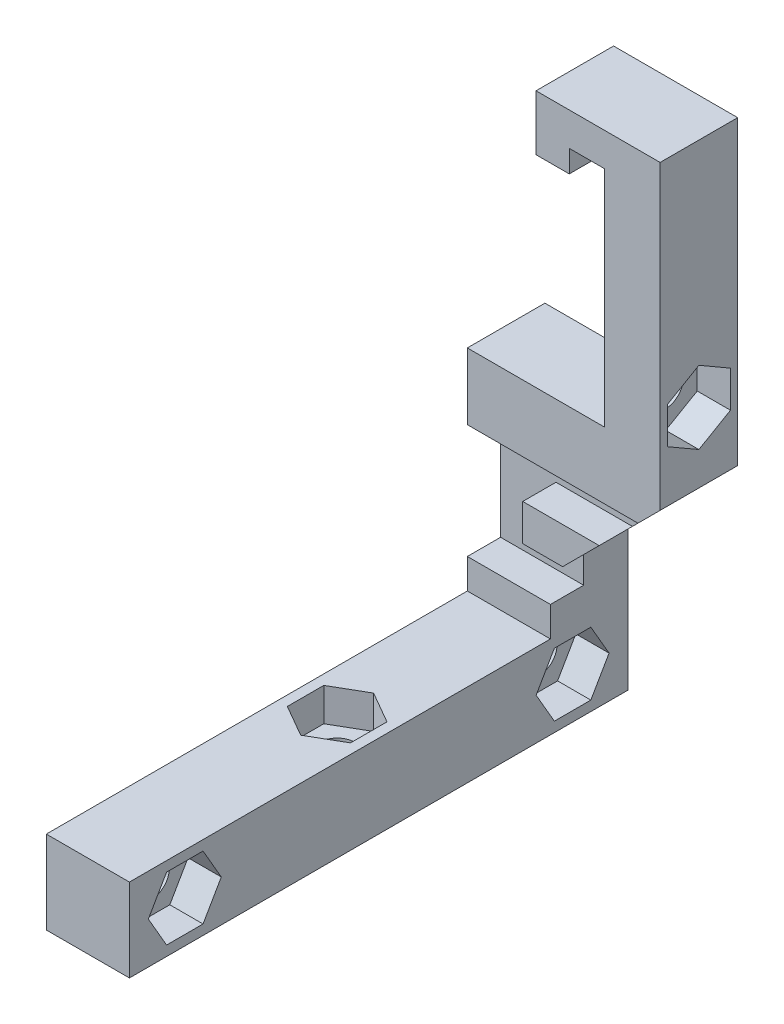
SolidWorks part; units mm, degrees
ref_plane "Alzado" through (0, 0, 0) normal (0, 0, 1) x (1, 0, 0)
ref_plane "Planta" through (0, 0, 0) normal (0, 1, 0) x (1, 0, 0)
ref_plane "Vista lateral" through (0, 0, 0) normal (1, 0, 0) x (0, 0, -1)
sketch "Croquis1" plane through (0, 0, 0) normal (0, 0, 1) x (1, 0, 0)
  line L0 (0, 26.5) -> (0, 0)
  line L1 (0, 0) -> (7.5, 0)
  line L2 (7.5, 0) -> (7.5, 12.6)
  line L3 (0, 26.5) -> (12.4, 26.5)
  line L4 (12.4, 26.5) -> (12.4, 46.7)
  line L5 (12.4, 46.7) -> (9.2, 46.7)
  line L6 (9.2, 46.7) -> (9.2, 44.7)
  line L7 (9.2, 44.7) -> (6.2, 44.7)
  line L8 (6.2, 44.7) -> (6.2, 49.7)
  line L9 (6.2, 49.7) -> (17.4, 49.7)
  line L10 (17.4, 49.7) -> (17.4, 22.5)
  line L11 (17.4, 22.5) -> (7.5, 12.6)
  dimension "D1" = 7.5
  dimension "D2" = 26.5
  dimension "D3" = 12.4
  dimension "D4" = 20.2
  dimension "D5" = 3.2
  dimension "D6" = 2
  dimension "D7" = 3
  dimension "D8" = 3
  dimension "D9" = 5
  dimension "D10" = 135
  dimension "D11" = 4
extrude "Saliente-Extruir1" add sketch "Croquis1" along normal blind 4
sketch "Croquis2" plane through (0, 0, 4) normal (0, 0, 1) x (1, 0, 0)
  line L0 (0, 0) -> (0, 10.2)
  line L1 (0, 10.2) -> (5, 10.2)
  line L2 (5, 10.2) -> (5, 20.5)
  line L3 (5, 20.5) -> (0, 20.5)
  line L4 (0, 20.5) -> (0, 26.5)
  line L12 (12.4, 26.5) -> (0, 26.5)
  line L13 (0, 26.5) -> (0, 0)
  line L14 (0, 0) -> (7.5, 0)
  line L15 (7.5, 0) -> (7.5, 12.6)
  line L16 (7.5, 12.6) -> (17.4, 22.5)
  line L17 (17.4, 22.5) -> (17.4, 49.7)
  line L18 (17.4, 49.7) -> (6.2, 49.7)
  line L19 (6.2, 49.7) -> (6.2, 44.7)
  line L20 (6.2, 44.7) -> (9.2, 44.7)
  line L21 (9.2, 44.7) -> (9.2, 46.7)
  line L22 (9.2, 46.7) -> (12.4, 46.7)
  line L23 (12.4, 46.7) -> (12.4, 26.5)
  line L24 (12.4, 26.5) -> (0, 26.5)
  line L25 (0, 26.5) -> (0, 0) construction
  line L26 (0, 0) -> (7.5, 0)
  line L27 (7.5, 0) -> (7.5, 12.6)
  line L28 (7.5, 12.6) -> (17.4, 22.5)
  line L29 (17.4, 22.5) -> (17.4, 49.7)
  line L30 (17.4, 49.7) -> (6.2, 49.7)
  line L31 (6.2, 49.7) -> (6.2, 44.7)
  line L32 (6.2, 44.7) -> (9.2, 44.7)
  line L33 (9.2, 44.7) -> (9.2, 46.7)
  line L34 (9.2, 46.7) -> (12.4, 46.7)
  line L35 (12.4, 46.7) -> (12.4, 26.5)
  dimension "D2" = 10.3
  dimension "D3" = 5
  dimension "D4" = 6
  dimension "D1" = 0
extrude "Saliente-Extruir2" add sketch "Croquis2" along normal blind 3
ref_plane "Plano1" through (0, 0, 45) normal (0, 0, -1) x (-1, 0, 0)
sketch "Croquis3" plane through (0, 0, 7) normal (0, 0, 1) x (1, 0, 0)
  line L0 (7.5, 0) -> (7.5, 12.6) construction
  line L1 (0, 0) -> (7.5, 0)
  line L2 (0, 0) -> (0, 7.5)
  line L3 (0, 7.5) -> (7.5, 7.5)
  line L4 (7.5, 0) -> (7.5, 7.5)
extrude "Saliente-Extruir3" add sketch "Croquis3" along normal up to surface (38 mm away) up to plane "Plano1"
sketch "Croquis4" plane through (12.4, 0, 0) normal (-1, 0, 0) x (0, 0, 1)
  line L0 (3.5, 26.5) -> (3.5, 28.8) construction
  line L1 (7, 26.5) -> (0, 26.5) construction
  circle A0 centre (3.5, 28.8) radius 1.6
  dimension "D1" = 3.2
  dimension "D2" = 2.3
extrude "Cortar-Extruir1" cut sketch "Croquis4" against normal up to next
sketch "Croquis5" plane through (17.4, 0, 0) normal (1, 0, 0) x (0, 0, -1)
  line L1 (-0.65, 30.4454) -> (-3.5, 32.0909)
  line L2 (-3.5, 32.0909) -> (-6.35, 30.4454)
  line L3 (-6.35, 30.4454) -> (-6.35, 27.1546)
  line L4 (-6.35, 27.1546) -> (-3.5, 25.5091)
  line L5 (-3.5, 25.5091) -> (-0.65, 27.1546)
  line L6 (-0.65, 27.1546) -> (-0.65, 30.4454)
  circle A0 centre (-3.5, 28.8) radius 2.85 construction
  dimension "D1" = 5.7
extrude "Cortar-Extruir2" cut sketch "Croquis5" against normal blind 3
sketch "Croquis6" plane through (0, 0, 0) normal (-1, 0, 0) x (0, 0, 1)
  line L0 (45, 3.75) -> (40, 3.75) construction
  line L1 (45, 0) -> (45, 7.5) construction
  line L2 (40, 3.75) -> (5, 3.75) construction
  line L3 (5, 3.75) -> (0, 3.75) construction
  line L4 (0, 26.5) -> (0, 0) construction
  circle A0 centre (5, 3.75) radius 1.6
  circle A1 centre (40, 3.75) radius 1.6
  dimension "D2" = 3.2
  dimension "D1" = 35
extrude "Cortar-Extruir3" cut sketch "Croquis6" against normal up to next
sketch "Croquis7" plane through (7.5, 0, 0) normal (1, 0, 0) x (0, 0, -1)
  line L1 (-3.3546, 6.6) -> (-6.6454, 6.6)
  line L2 (-6.6454, 6.6) -> (-8.2909, 3.75)
  line L3 (-8.2909, 3.75) -> (-6.6454, 0.9)
  line L4 (-6.6454, 0.9) -> (-3.3546, 0.9)
  line L5 (-3.3546, 0.9) -> (-1.7091, 3.75)
  line L6 (-1.7091, 3.75) -> (-3.3546, 6.6)
  line L7 (-38.3546, 6.6) -> (-41.6454, 6.6)
  line L8 (-41.6454, 6.6) -> (-43.2909, 3.75)
  line L9 (-43.2909, 3.75) -> (-41.6454, 0.9)
  line L10 (-41.6454, 0.9) -> (-38.3546, 0.9)
  line L11 (-38.3546, 0.9) -> (-36.7091, 3.75)
  line L12 (-36.7091, 3.75) -> (-38.3546, 6.6)
  circle A0 centre (-5, 3.75) radius 2.85 construction
  circle A1 centre (-40, 3.75) radius 2.85 construction
  dimension "D1" = 5.7
extrude "Cortar-Extruir4" cut sketch "Croquis7" against normal blind 3
sketch "Croquis8" plane through (0, 0, 0) normal (0, -1, 0) x (1, 0, 0)
  line L0 (3.75, 0) -> (3.75, 45) construction
  line L1 (0, 0) -> (7.5, 0) construction
  line L2 (7.5, 45) -> (0, 45) construction
  circle A0 centre (3.75, 22.5) radius 1.6
  dimension "D1" = 3.2
extrude "Cortar-Extruir5" cut sketch "Croquis8" against normal up to next
sketch "Croquis9" plane through (0, 7.5, 0) normal (0, 1, 0) x (1, 0, 0)
  line L1 (0.9, -20.8546) -> (0.9, -24.1454)
  line L2 (0.9, -24.1454) -> (3.75, -25.7909)
  line L3 (3.75, -25.7909) -> (6.6, -24.1454)
  line L4 (6.6, -24.1454) -> (6.6, -20.8546)
  line L5 (6.6, -20.8546) -> (3.75, -19.2091)
  line L6 (3.75, -19.2091) -> (0.9, -20.8546)
  circle A0 centre (3.75, -22.5) radius 2.85 construction
  dimension "D1" = 5.7
extrude "Cortar-Extruir6" cut sketch "Croquis9" against normal blind 3
sketch "Croquis10" plane through (5, 0, 0) normal (-1, 0, 0) x (0, 0, 1)
  line L0 (7, 20.5) -> (7, 10.2) construction
  line L1 (4, 10.2) -> (7, 10.2)
  line L2 (4, 10.2) -> (4, 13.7)
  line L3 (4, 13.7) -> (7, 13.7)
  line L4 (7, 10.2) -> (7, 13.7)
  line L6 (4, 20.5) -> (7, 20.5)
  line L7 (4, 20.5) -> (4, 17)
  line L8 (4, 17) -> (7, 17)
  line L9 (7, 20.5) -> (7, 17)
  dimension "D1" = 3.5
  dimension "D2" = 3.5
extrude "Cortar-Extruir7" cut sketch "Croquis10" against normal up to next
